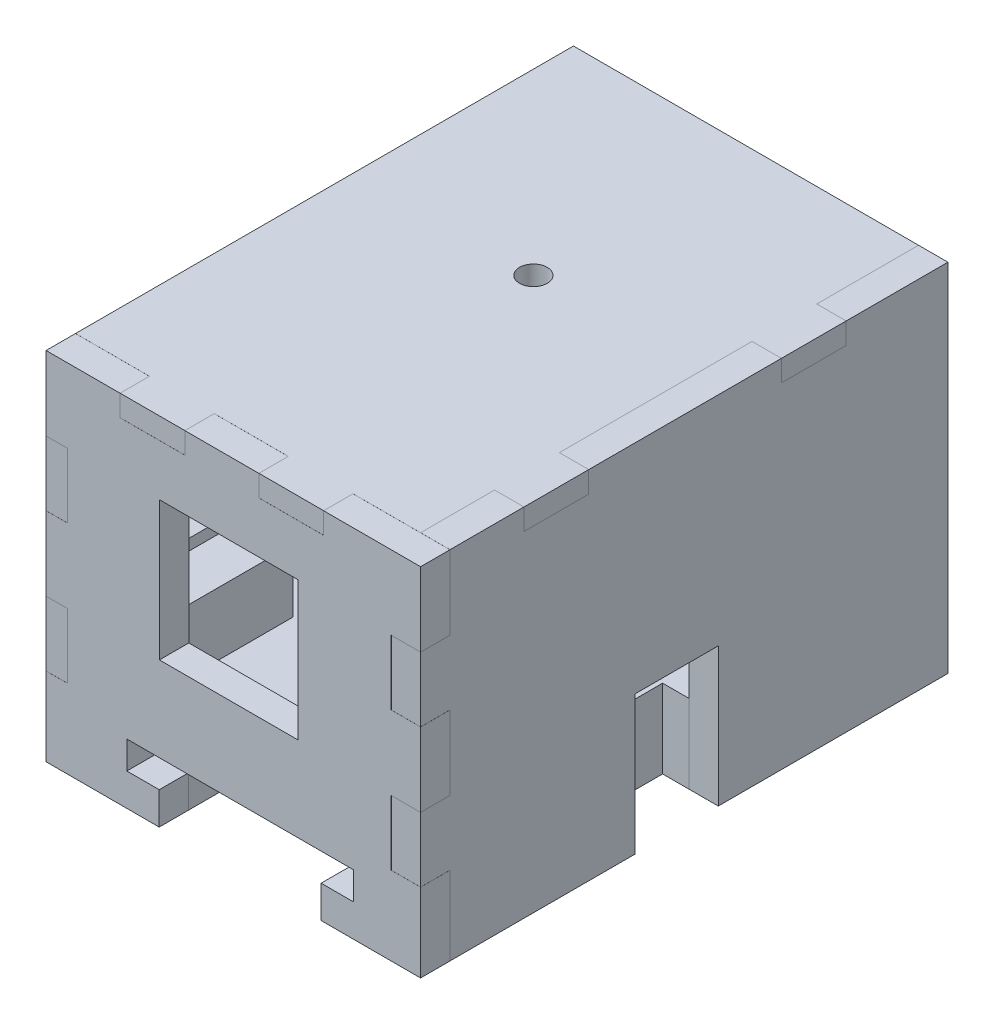
SolidWorks part; units mm, degrees
ref_plane "Front Plane" through (0, 0, 0) normal (0, 0, 1) x (1, 0, 0)
ref_plane "Top Plane" through (0, 0, 0) normal (0, 1, 0) x (1, 0, 0)
ref_plane "Right Plane" through (0, 0, 0) normal (1, 0, 0) x (0, 0, -1)
ref_plane "Plane3" through (0, 0, 53.83) normal (0, 0, 1) x (1, 0, 0)
sketch "Sketch1" plane through (0, 0, 0) normal (1, 0, 0) x (0, 0, -1)
  line L0 (0, 40.694) -> (0, 2.194)
  line L1 (0, 1.7462) -> (0, -1.7462) construction
  line L8 (-53.825, 2.194) -> (-53.825, 40.694)
  line L13 (-53.825, 40.694) -> (0, 40.694)
  line L19 (-53.825, 2.194) -> (0, 2.194)
  dimension "D1" = 0
extrude "main extrude" add sketch "Sketch1" along normal blind 2.3
sketch "Sketch3" plane through (2.3, 0, 0) normal (1, 0, 0) x (0, 0, -1)
  line L4 (-2.3, 38.394) -> (-2.3, 10.694)
  line L8 (-53.825, 38.394) -> (-2.3, 38.394)
  line L13 (-53.825, 40.694) -> (-53.825, 38.394)
  line L14 (-53.825, 40.694) -> (0, 40.694)
  line L15 (0, 40.694) -> (0, 2.194)
  line L16 (0, 2.194) -> (-53.825, 2.194)
  line L19 (-53.825, 10.694) -> (-2.3, 10.694)
  line L20 (-53.825, 40.694) -> (-53.825, 2.194) construction
  line L22 (-53.825, 10.694) -> (-53.825, 2.194)
  dimension "D1" = 2.3
  dimension "D2" = 2.3
extrude "walls" add sketch "Sketch3" along normal blind 35
sketch "Sketch36" plane through (0, 0, 53.825) normal (0, 0, 1) x (1, 0, 0)
  line L0 (37.3, 40.694) -> (0, 40.694) construction
  line L1 (8, 40.694) -> (15, 40.694)
  line L2 (8, 40.694) -> (8, 38.394)
  line L3 (8, 38.394) -> (15, 38.394)
  line L4 (15, 40.694) -> (15, 38.394)
  line L5 (37.3, 38.394) -> (2.3, 38.394) construction
  line L6 (37.3, 38.394) -> (2.3, 38.394) construction
  line L7 (23, 40.694) -> (30, 40.694)
  line L8 (23, 40.694) -> (23, 38.394)
  line L9 (23, 38.394) -> (30, 38.394)
  line L10 (30, 40.694) -> (30, 38.394)
  line L11 (0, 40.694) -> (0, 2.194) construction
  line L12 (0, 32.694) -> (2.3, 32.694)
  line L13 (0, 32.694) -> (0, 25.694)
  line L14 (0, 25.694) -> (2.3, 25.694)
  line L15 (2.3, 32.694) -> (2.3, 25.694)
  line L16 (2.3, 38.394) -> (2.3, 10.694) construction
  line L17 (2.3, 38.394) -> (2.3, 10.694) construction
  line L18 (0, 17.694) -> (2.3, 17.694)
  line L19 (0, 17.694) -> (0, 10.694)
  line L20 (0, 10.694) -> (2.3, 10.694)
  line L21 (2.3, 17.694) -> (2.3, 10.694)
  dimension "D1" = 8
  dimension "D2" = 8
  dimension "D3" = 7
  dimension "D4" = 7
  dimension "D5" = 7
  dimension "D6" = 7
  dimension "D7" = 8
  dimension "D8" = 8
extrude "Puzzle (main walls)" add sketch "Sketch36" along normal blind 3.175
sketch "Sketch25" plane through (0, 0, 2.3) normal (0, 0, 1) x (1, 0, 0)
  line L1 (2.3, 10.694) -> (12.703, 10.694)
  line L2 (2.3, 10.694) -> (2.3, 17.2991)
  line L3 (2.3, 17.2991) -> (12.703, 17.2991)
  line L4 (12.703, 10.694) -> (12.703, 17.2991)
extrude "Wire Hole" cut sketch "Sketch25" against normal through all
sketch "Sketch19" plane through (0, 10.694, 0) normal (0, 1, 0) x (1, 0, 0)
  line L16 (37.3, -38.625) -> (37.3, -53.825)
  line L18 (30.8, -53.825) -> (37.3, -53.825)
  line L27 (37.3, 0) -> (37.3, -53.825) construction
  line L40 (30.8, -53.825) -> (30.8, -38.625)
  line L41 (30.8, -38.625) -> (37.3, -38.625)
  line L47 (2.3, -53.825) -> (8.3, -53.825)
  line L48 (2.3, -53.825) -> (2.3, -38.625)
  line L49 (2.3, -38.625) -> (8.3, -38.625)
  line L50 (8.3, -53.825) -> (8.3, -38.625)
extrude "IR mount" add sketch "Sketch19" along normal blind 7
sketch "Sketch24" plane through (0, 0, 53.83) normal (0, 0, 1) x (1, 0, 0)
  line L0 (37.3, 2.194) -> (0, 2.194) construction
  line L1 (12.23, 2.194) -> (29.73, 2.194)
  line L2 (12.23, 2.194) -> (12.23, 5.694)
  line L4 (29.73, 2.194) -> (29.73, 5.694)
  line L5 (12.23, 5.694) -> (8.73, 5.694)
  line L6 (8.73, 5.694) -> (8.73, 8.694)
  line L9 (33.23, 8.694) -> (33.23, 5.694)
  line L10 (33.23, 5.694) -> (29.73, 5.694)
  line L11 (0, 10.694) -> (0, 2.194) construction
  line L12 (8.73, 8.694) -> (33.23, 8.694)
  dimension "D1" = 8.73
  dimension "D2" = 0
  dimension "D3" = 3.5
  dimension "D4" = 3
  dimension "D5" = 3
  dimension "D6" = 3.5
  dimension "D7" = 3.5
  dimension "D8" = 3.5
  dimension "D9" = 17.5
extrude "Magnet Mount Hole" cut sketch "Sketch24" against normal blind 51.83
sketch "Sketch40" plane through (0, 40.694, 0) normal (0, 1, 0) x (1, 0, 0)
  line L0 (37.3, 0) -> (37.3, -53.825) construction
  line L1 (0, 0) -> (0, -53.825) construction
  circle A0 centre (19.3, -23.6329) radius 1.5
  dimension "D1" = 3
  dimension "D2" = 18
  dimension "D3" = 19.3
extrude "LED Space" cut sketch "Sketch40" against normal blind 3
sketch "Sketch42" plane through (37.3, 0, 0) normal (1, 0, 0) x (0, 0, -1)
  line L0 (0, 40.694) -> (-53.825, 40.694) construction
  line L1 (-45.825, 40.694) -> (-38.825, 40.694)
  line L2 (-45.825, 40.694) -> (-45.825, 38.394)
  line L3 (-45.825, 38.394) -> (-38.825, 38.394)
  line L4 (-38.825, 40.694) -> (-38.825, 38.394)
  line L5 (-53.825, 38.394) -> (-2.3, 38.394) construction
  line L6 (-53.825, 38.394) -> (-2.3, 38.394) construction
  line L7 (-18, 40.694) -> (-11, 40.694)
  line L8 (-18, 40.694) -> (-18, 38.394)
  line L9 (-18, 38.394) -> (-11, 38.394)
  line L10 (-11, 40.694) -> (-11, 38.394)
  line L11 (-53.825, 40.694) -> (-53.825, 38.394) construction
  line L12 (0, 2.194) -> (0, 40.694) construction
  dimension "D1" = 8
  dimension "D2" = 7
  dimension "D3" = 7
  dimension "D4" = 11
extrude "Boss-Extrude15" add sketch "Sketch42" along normal blind 3.175
sketch "Sketch44" plane through (0, 17.694, 0) normal (0, 1, 0) x (1, 0, 0)
  line L1 (2.3, -38.625) -> (8.3, -38.625)
  line L2 (2.3, -38.625) -> (2.3, -53.825)
  line L3 (2.3, -53.825) -> (8.3, -53.825)
  line L4 (8.3, -38.625) -> (8.3, -53.825)
  line L5 (30.8, -38.625) -> (37.3, -38.625)
  line L6 (30.8, -38.625) -> (30.8, -53.825)
  line L7 (30.8, -53.825) -> (37.3, -53.825)
  line L8 (37.3, -38.625) -> (37.3, -53.825)
extrude "Boss-Extrude16" add sketch "Sketch44" along normal blind 6
sketch "Sketch45" plane through (0, 0, 53.825) normal (0, 0, 1) x (1, 0, 0)
  line L0 (30.8, 23.694) -> (30.8, 10.694) construction
  line L1 (30.8, 22.494) -> (35.8, 22.494)
  line L2 (30.8, 22.494) -> (30.8, 17.494)
  line L3 (30.8, 17.494) -> (35.8, 17.494)
  line L4 (35.8, 22.494) -> (35.8, 17.494)
  line L5 (8.3, 23.694) -> (8.3, 10.694) construction
  line L6 (8.3, 22.494) -> (3.3, 22.494)
  line L7 (8.3, 22.494) -> (8.3, 17.494)
  line L8 (8.3, 17.494) -> (3.3, 17.494)
  line L9 (3.3, 22.494) -> (3.3, 17.494)
  line L10 (2.3, 23.694) -> (8.3, 23.694) construction
  line L11 (30.8, 23.694) -> (37.3, 23.694) construction
  dimension "D1" = 1.2
  dimension "D2" = 1.2
  dimension "D3" = 5
  dimension "D4" = 5
  dimension "D5" = 5
  dimension "5" = 5
extrude "IR placement" cut sketch "Sketch45" against normal up to surface (15.2 mm away) up to face at (5.3, 17.194, 38.625)
sketch "Sketch47" plane through (0, 0, 0) normal (0, 0, -1) x (-1, 0, 0)
  circle A0 centre (-21.019, 5.2627) radius 2.5
  dimension "D1" = 5
extrude "Cut-Extrude2" cut sketch "Sketch47" against normal up to surface (2 mm away) up to face at (20.98, 5.569, 2)
sketch "Sketch48" plane through (0, 2.194, 0) normal (0, -1, 0) x (1, 0, 0)
  line L0 (0, 53.825) -> (0, 0) construction
  line L1 (0, 33.825) -> (7, 33.825)
  line L2 (0, 33.825) -> (0, 24.825)
  line L3 (0, 24.825) -> (7, 24.825)
  line L4 (7, 33.825) -> (7, 24.825)
  line L5 (34.4625, 33.825) -> (41.4625, 33.825)
  line L6 (34.4625, 33.825) -> (34.4625, 24.825)
  line L7 (34.4625, 24.825) -> (41.4625, 24.825)
  line L8 (41.4625, 33.825) -> (41.4625, 24.825)
  line L9 (37.3, 53.825) -> (29.73, 53.825) construction
  line L10 (12.23, 53.825) -> (0, 53.825) construction
  dimension "D1" = 20
  dimension "D2" = 20
  dimension "D3" = 9
extrude "Cut-Extrude3" cut sketch "Sketch48" against normal blind 15
ref_plane "Plane5" through (37.3, 0, 0) normal (1, 0, 0) x (0, 0, -1)
sketch "Sketch6" plane through (0, 0, 53.83) normal (0, 0, 1) x (1, 0, 0)
  line L2 (0, 40.694) -> (0, 2.194)
  line L6 (0, 40.694) -> (40.48, 40.694)
  line L7 (40.48, 40.694) -> (40.48, 2.194)
  line L8 (0, 2.194) -> (40.48, 2.194)
extrude "front lid" add sketch "Sketch6" along normal blind 3.175 separate body
sketch "Sketch7" plane through (0, 0, 57.005) normal (0, 0, 1) x (1, 0, 0)
  line L0 (0, 2.194) -> (40.48, 2.194) construction
  line L6 (0, -21.175) -> (0, 21.175) construction
  line L10 (19.75, 17.854) -> (27.25, 17.854)
  line L11 (19.75, 17.854) -> (12.25, 17.854)
  line L12 (12.25, 17.854) -> (12.25, 32.854)
  line L13 (12.25, 32.854) -> (27.25, 32.854)
  line L14 (27.25, 17.854) -> (27.25, 32.854)
  circle A0 centre (19.75, 25.354) radius 7.5 construction
  point P12 (19.75, 25.354)
  dimension "D1" = 15
  dimension "D2" = 19.75
  dimension "D4" = 15.66
extrude "nosepoke hole" cut sketch "Sketch7" against normal blind 3.175
sketch "Sketch34" plane through (0, 0, 57.005) normal (0, 0, 1) x (1, 0, 0)
  line L0 (0, 40.694) -> (0, 2.194) construction
  line L1 (0, 32.694) -> (2.3, 32.694)
  line L2 (0, 32.694) -> (0, 25.694)
  line L3 (0, 25.694) -> (2.3, 25.694)
  line L4 (2.3, 32.694) -> (2.3, 25.694)
  line L9 (40.48, 40.694) -> (0, 40.694) construction
  line L10 (8, 40.694) -> (15, 40.694)
  line L11 (8, 40.694) -> (8, 38.394)
  line L12 (8, 38.394) -> (15, 38.394)
  line L13 (15, 40.694) -> (15, 38.394)
  line L14 (23, 40.694) -> (30, 40.694)
  line L15 (23, 40.694) -> (23, 38.394)
  line L16 (23, 38.394) -> (30, 38.394)
  line L17 (30, 40.694) -> (30, 38.394)
  line L23 (40.48, 2.194) -> (40.48, 40.694) construction
  line L24 (0, 17.694) -> (2.3, 17.694)
  line L25 (0, 17.694) -> (0, 10.694)
  line L26 (0, 10.694) -> (2.3, 10.694)
  line L27 (2.3, 17.694) -> (2.3, 10.694)
  line L32 (40.48, 32.694) -> (37.305, 32.694)
  line L33 (40.48, 32.694) -> (40.48, 25.694)
  line L34 (40.48, 25.694) -> (37.305, 25.694)
  line L35 (37.305, 32.694) -> (37.305, 25.694)
  line L37 (40.48, 17.694) -> (37.305, 17.694)
  line L38 (40.48, 17.694) -> (40.48, 10.694)
  line L39 (40.48, 10.694) -> (37.305, 10.694)
  line L40 (37.305, 17.694) -> (37.305, 10.694)
  point P16 (15, 39.544)
  dimension "D1" = 8
  dimension "D2" = 8
  dimension "D3" = 8
  dimension "D4" = 8
  dimension "D5" = 8
  dimension "D6" = 7
  dimension "D7" = 7
  dimension "D8" = 2.3
  dimension "D9" = 8
extrude "Puzzle (Front Lid)" cut sketch "Sketch34" against normal up to surface (3.175 mm away) up to face at (19.75, 25.354, 53.83)
sketch "Sketch46" plane through (0, 0, 57.005) normal (0, 0, 1) x (1, 0, 0)
  line L0 (12.23, 2.194) -> (29.73, 2.194)
  line L1 (12.23, 2.194) -> (12.23, 5.694)
  line L2 (29.73, 2.194) -> (29.73, 5.694)
  line L3 (12.23, 5.694) -> (8.73, 5.694)
  line L4 (8.73, 5.694) -> (8.73, 8.694)
  line L5 (33.23, 8.694) -> (33.23, 5.694)
  line L6 (33.23, 5.694) -> (29.73, 5.694)
  line L7 (8.73, 8.694) -> (33.23, 8.694)
  line L8 (0, 10.694) -> (0, 2.194) construction
  line L10 (0, 2.194) -> (40.48, 2.194) construction
  dimension "D1" = 8.73
  dimension "D3" = 3
  dimension "D4" = 3.5
  dimension "D5" = 0
  dimension "D6" = 3.5
  dimension "D7" = 3
  dimension "D8" = 3.5
  dimension "D9" = 3.5
  dimension "D10" = 17.5
extrude "magnet mount front lid" cut sketch "Sketch46" against normal up to surface (3.175 mm away) up to face at (19.7607, 26.7583, 53.83)
sketch "Lever Space in Operant (reference)" [suppressed] plane through (0, 0, 57.005) normal (0, 0, 1) x (1, 0, 0)
  line L1 (2.88, 34.514) -> (34.4305, 34.514) construction
  line L2 (2.88, 34.514) -> (2.88, 17.854) construction
  line L3 (2.88, 17.854) -> (34.4305, 17.854) construction
  line L4 (34.4305, 34.514) -> (34.4305, 17.854) construction
  line L7 (0, -21.175) -> (0, 21.175) construction
  line L8 (2.3, 10.694) -> (2.3, 38.394) construction
  line L9 (12.25, 32.854) -> (27.25, 32.854) construction
  line L10 (12.25, 32.854) -> (12.25, 17.854) construction
  line L11 (12.25, 17.854) -> (27.25, 17.854) construction
  line L12 (27.25, 32.854) -> (27.25, 17.854) construction
  line L14 (0, 2.194) -> (40.48, 2.194) construction
  dimension "D1" = 15.66
  dimension "D2" = 2.88
  dimension "D3" = 31.5505
  dimension "D4" = 16.66
ref_plane "contact face with wall" through (0, 0, 57.005) normal (0, 0, 1) x (1, 0, 0)
sketch "Acrylic Guard (reference)" plane through (0, 0, 53.83) normal (0, 0, -1) x (-1, 0, 0)
  line L0 (7.75, 32.854) -> (50007.75, 32.854) construction
  line L1 (-27.25, 32.854) -> (-27.25, 17.854)
  line L2 (-27.25, 17.854) -> (-12.25, 17.854)
  line L3 (-12.25, 17.854) -> (-12.25, 32.854)
  line L4 (-12.25, 32.854) -> (-9.25, 32.854)
  line L5 (-9.25, 32.854) -> (-9.25, 14.854)
  line L6 (-9.25, 14.854) -> (-30.25, 14.854)
  line L7 (-30.25, 14.854) -> (-30.25, 32.854)
  line L8 (-30.25, 32.854) -> (-27.25, 32.854)
  dimension "D1" = 3
sketch "Sketch20" plane through (37.3, 0, 0) normal (1, 0, 0) x (0, 0, -1)
  line L1 (-53.825, 40.694) -> (0, 40.694)
  line L2 (-53.825, 40.694) -> (-53.825, 2.194)
  line L3 (-53.825, 2.194) -> (0, 2.194)
  line L4 (0, 40.694) -> (0, 2.194)
extrude "Side main" add sketch "Sketch20" along normal blind 3.175 separate body
sketch "Sketch37" plane through (0, 0, 53.825) normal (0, 0, 1) x (1, 0, 0)
  line L0 (37.3, 40.694) -> (37.3, 2.194) construction
  line L1 (37.3, 32.694) -> (40.475, 32.694)
  line L2 (37.3, 32.694) -> (37.3, 25.694)
  line L3 (37.3, 25.694) -> (40.475, 25.694)
  line L4 (40.475, 32.694) -> (40.475, 25.694)
  line L5 (40.475, 40.694) -> (40.475, 2.194) construction
  line L6 (40.475, 40.694) -> (37.3, 40.694) construction
  line L7 (37.3, 17.694) -> (40.475, 17.694)
  line L8 (37.3, 17.694) -> (37.3, 10.694)
  line L9 (37.3, 10.694) -> (40.475, 10.694)
  line L10 (40.475, 17.694) -> (40.475, 10.694)
  dimension "D1" = 8
  dimension "D2" = 7
  dimension "D3" = 8
  dimension "D4" = 7
extrude "Puzzle (side part)" add sketch "Sketch37" along normal blind 3.175
sketch "Sketch41" plane through (40.475, 0, 0) normal (1, 0, 0) x (0, 0, -1)
  line L0 (0, 40.694) -> (-53.825, 40.694) construction
  line L1 (-45.825, 40.694) -> (-38.825, 40.694)
  line L2 (-45.825, 40.694) -> (-45.825, 38.394)
  line L3 (-45.825, 38.394) -> (-38.825, 38.394)
  line L4 (-38.825, 40.694) -> (-38.825, 38.394)
  line L5 (-53.825, 40.694) -> (-53.825, 32.694) construction
  line L6 (-18, 40.694) -> (-11, 40.694)
  line L7 (-18, 40.694) -> (-18, 38.394)
  line L8 (-18, 38.394) -> (-11, 38.394)
  line L9 (-11, 40.694) -> (-11, 38.394)
  line L10 (0, 2.194) -> (0, 40.694) construction
  dimension "D1" = 8
  dimension "D2" = 11
  dimension "D3" = 7
extrude "Cut-Extrude1" cut sketch "Sketch41" against normal up to surface (3.175 mm away) up to face at (37.3, 21.6106, 45.9125)
sketch "Sketch49" plane through (0, 2.194, 0) normal (0, -1, 0) x (1, 0, 0)
  line L0 (40.475, 53.825) -> (40.475, 0) construction
  line L1 (40.475, 33.825) -> (33.475, 33.825)
  line L2 (40.475, 33.825) -> (40.475, 24.825)
  line L3 (40.475, 24.825) -> (33.475, 24.825)
  line L4 (33.475, 33.825) -> (33.475, 24.825)
  line L5 (40.475, 53.825) -> (37.3, 53.825) construction
  dimension "D1" = 20
extrude "Cut-Extrude4" cut sketch "Sketch49" against normal blind 15
